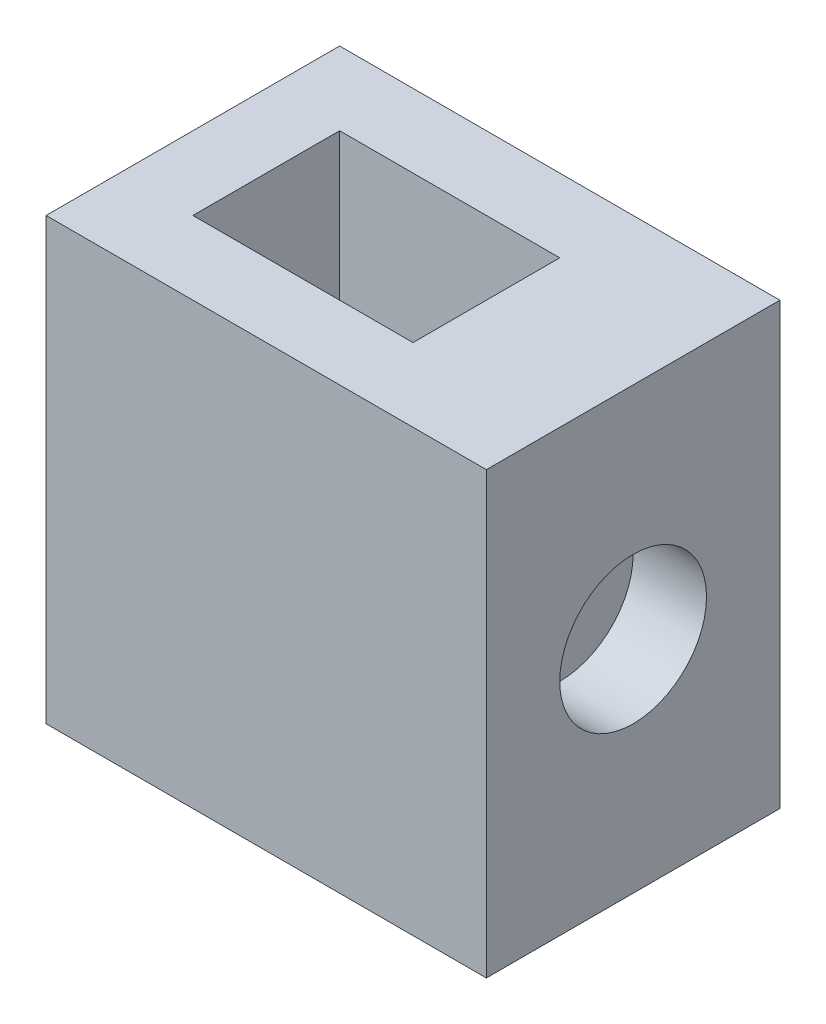
SolidWorks part; units mm, degrees
ref_plane "Front Plane" through (0, 0, 0) normal (0, 0, 1) x (1, 0, 0)
ref_plane "Top Plane" through (0, 0, 0) normal (0, 1, 0) x (1, 0, 0)
ref_plane "Right Plane" through (0, 0, 0) normal (1, 0, 0) x (0, 0, -1)
sketch "Sketch1" plane through (0, 0, 0) normal (0, 1, 0) x (1, 0, 0)
  line L1 (0, 0) -> (76.2, 0)
  line L2 (0, 0) -> (0, 50.8)
  line L3 (0, 50.8) -> (76.2, 50.8)
  line L4 (76.2, 0) -> (76.2, 50.8)
  dimension "D1" = 50.8
  dimension "D2" = 76.2
extrude "Boss-Extrude1" add sketch "Sketch1" along normal blind 76.2
sketch "Sketch2" plane through (0, 76.2, 0) normal (0, 1, 0) x (1, 0, 0)
  line L1 (12.7, 38.1) -> (50.8, 38.1)
  line L2 (12.7, 38.1) -> (12.7, 12.7)
  line L3 (12.7, 12.7) -> (50.8, 12.7)
  line L4 (50.8, 38.1) -> (50.8, 12.7)
  dimension "D1" = 12.7
  dimension "D2" = 12.7
  dimension "D3" = 25.4
  dimension "D4" = 38.1
extrude "Cut-Extrude1" cut sketch "Sketch2" against normal blind 25.4
sketch "Sketch3" plane through (76.2, 0, 0) normal (1, 0, 0) x (0, 0, -1)
  circle A0 centre (25.4, 38.1) radius 12.7
  dimension "D2" = 25.4
  dimension "D1" = 25.4
  dimension "D3" = 38.1
extrude "Cut-Extrude3" cut sketch "Sketch3" against normal blind 12.7
